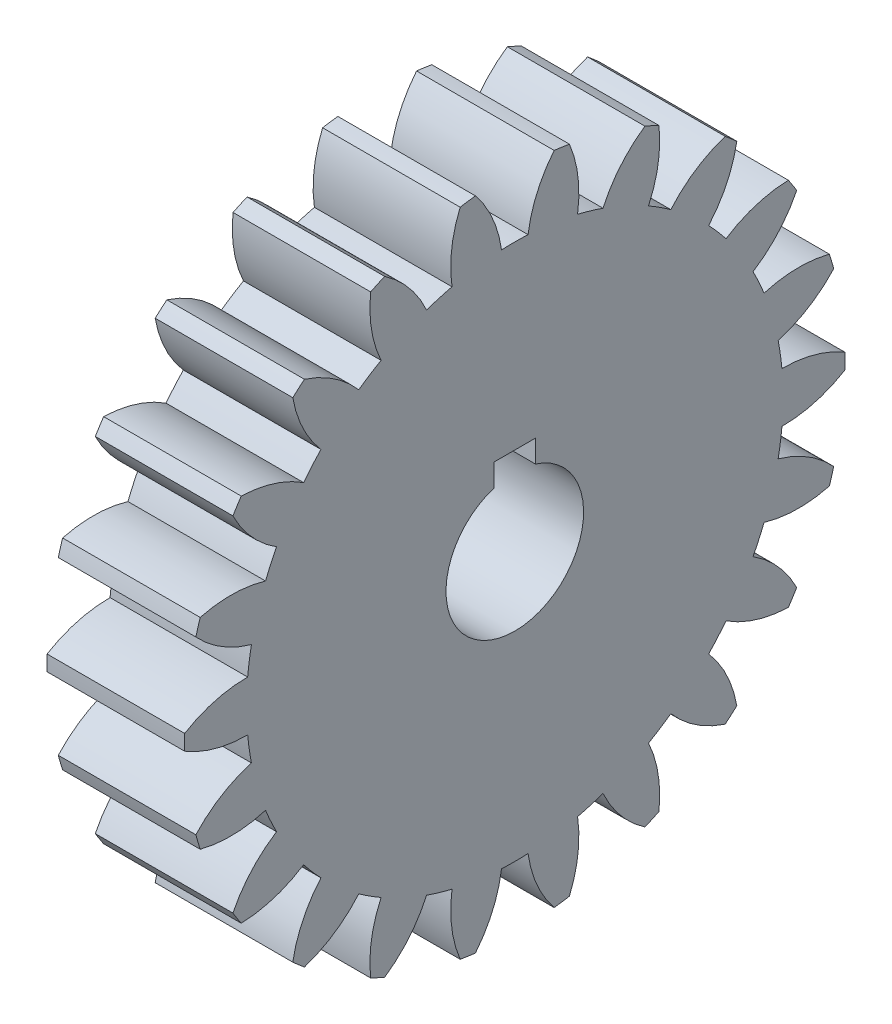
SolidWorks part; units mm, degrees
ref_plane "Plane1" through (0, 0, 0) normal (0, 0, 1) x (1, 0, 0)
ref_plane "Plane2" through (0, 0, 0) normal (0, 1, 0) x (1, 0, 0)
ref_plane "Plane3" through (0, 0, 0) normal (1, 0, 0) x (0, 0, -1)
sketch "HoldingSke" plane through (0, 0, 0) normal (0, 1, 0) x (1, 0, 0)
  line L0 (0, 0) -> (0.2318, -0.0937)
  line L1 (-15, 0) -> (100, 0) construction
  line L2 (0, 0) -> (-2.1039, 2.3779)
  line L3 (0, 0) -> (-11.863, 4.5341)
  line L4 (0, 0) -> (8.0072, 3.2351)
  line L5 (0, 0) -> (-46.8476, -17.4728)
  line L6 (0, 0) -> (-16.5793, -11.1861)
  line L7 (-2.1039, 2.3779) -> (8.6586, 51.2059)
  line L8 (-76.2, 54.61) -> (-73.4, 54.61)
  line L9 (-71.009, 38.7566) -> (-53.1078, 45.2721)
  line L10 (-76.2, 71.12) -> (104.1128, 71.12)
  line L11 (0, 0) -> (-20, 0)
  line L12 (-76.2, 101.6) -> (-76.073, 101.6)
  line L13 (24.9733, 27.94) -> (52.9518, 28.4284)
  line L14 (24.9733, 27.94) -> (24.9743, 27.94)
  line L15 (24.9733, 27.94) -> (100.4006, 29.5858)
  line L16 (-63.627, -4) -> (-12.827, -4)
  circle A0 centre (0, 0) radius 10
  circle A1 centre (0, 0) radius 37.5
  circle A2 centre (0, 0) radius 37.5
  circle A3 centre (0, 0) radius 10
  dimension "MHD" = 75
  dimension "Hub_dia" = 75
  dimension "Bore" = 20
  dimension "MBD" = 20
  dimension "Num_teeth" = 22
  dimension "Pitch" = 0.25
  dimension "Overall_len" = 50
  dimension "Show_teeth" = 22
  dimension "Thickness" = 20
  dimension "OAL" = 50.0001
  dimension "T_dim" = 2.8
  dimension "Ap" = 20
  dimension "H" = 19.05
  dimension "Pitch_radius" = 180.3128
  dimension "Width" = 20
  dimension "Backlash" = 0.127
  dimension "Addendum_fac" = 1
  dimension "Dedendum_fac" = 1.25
  dimension "Clearance_fac" = 0.25
  dimension "Dedendum_add" = 0.001
  dimension "Module" = 4
sketch "BasProSke" plane through (0, 0, 0) normal (0, 1, 0) x (1, 0, 0)
  line L0 (-10, 0) -> (60, 0) construction
  line L1 (0, 0) -> (0, 48)
  line L2 (0, 0) -> (20, 0)
  line L3 (20, 0) -> (20, 48)
  line L4 (20, 48) -> (0, 48)
  dimension "Thickness" = 20
  dimension "Diameter" = 96
revolve "Base-Revolve" add sketch "BasProSke" angle 360 about L0
sketch "TooCutSke" plane through (0, 0, 0) normal (1, 0, 0) x (0, 0, -1)
  line L1 (0, 0) -> (0, 107) construction
  line L2 (0, 0) -> (-3.3611, 43.8714) construction
  line L3 (0, 0) -> (-12.4962, 86.9127) construction
  line L4 (-3.3611, 43.8714) -> (-6.2481, 43.4564) construction
  arc A0 (1.9256, 38.9514) -> (-1.9256, 38.9514) centre (0, 0) ccw
  arc A1 (5.7387, 47.6813) -> (-5.7387, 47.6813) centre (0, 0) ccw
  circle A2 centre (0, 0) radius 44 construction
  circle A3 centre (0, 0) radius 41.3465 construction
  arc A4 (-1.9256, 38.9514) -> (-5.7387, 47.6813) centre (-19.3589, 36.5344) ccw
  arc A5 (5.7387, 47.6813) -> (1.9256, 38.9514) centre (19.3589, 36.5344) ccw
  dimension "Root_dia" = 77.998
  dimension "Overcut_dia" = 96.0508
  dimension "Pitch_dia" = 88
  dimension "Base_dia" = 82.693
  dimension "Flank_rad" = 17.6
  dimension "Half_ang" = 8.182
  dimension "Half_CT" = 2.9167
extrude "ToothCut" cut sketch "TooCutSke" along normal through all
fillet "Breaks" [suppressed] radius 0.08
fillet "RootFillets" [suppressed] radius 1.001
pattern_circular "TeethCuts" count 22 every 16.364 about axis through (-10, 0, 0) along (1, 0, 0) of "ToothCut", "RootFillets", "Breaks"
sketch "HubNeaOneSke" plane through (0, 0, 0) normal (-1, 0, 0) x (0, 0, 1)
  circle A0 centre (0, 0) radius 37.5
  dimension "Diameter" = 75
extrude "HubNearOne" [suppressed] add sketch "HubNeaOneSke" along normal blind 30.0001
sketch "HubNeaBotSke" plane through (0, 0, 0) normal (-1, 0, 0) x (0, 0, 1)
  circle A0 centre (0, 0) radius 37.5
  dimension "Diameter" = 75
extrude "HubNearBoth" [suppressed] add sketch "HubNeaBotSke" along normal blind 15
ref_plane "FarPln" through (20, 0, 0) normal (1, 0, 0) x (0, 0, -1)
sketch "HubFarSke" plane through (20, 0, 0) normal (1, 0, 0) x (0, 0, -1)
  circle A0 centre (0, 0) radius 37.5
  dimension "Diameter" = 75
extrude "HubFar" [suppressed] add sketch "HubFarSke" along normal blind 15
sketch "BorSke" plane through (0, 0, 0) normal (1, 0, 0) x (0, 0, -1)
  circle A0 centre (0, 0) radius 10
  dimension "Diameter" = 20
extrude "Bore" cut sketch "BorSke" along normal mid plane 100.0001
sketch "KeySke" plane through (0, 0, 0) normal (1, 0, 0) x (0, 0, -1)
  line L0 (-3, 0) -> (-3, 12.8)
  line L1 (-3, 12.8) -> (3, 12.8)
  line L2 (3, 12.8) -> (3, 0)
  line L3 (0, 0) -> (0, 34) construction
  line L4 (-3, 0) -> (3, 0)
  dimension "Offset" = 12.8
  dimension "Width" = 6
extrude "Keyway" cut sketch "KeySke" along normal mid plane 100.0001
pattern_circular "Keyway2" [suppressed] count 2 every 90 about axis through (-10, 0, 0) along (1, 0, 0)
sketch "Çizim1" plane through (20, 0, 0) normal (1, 0, 0) x (0, 0, -1)
  circle A0 centre (0, 0) radius 44 construction
  dimension "D1" = 88
equation "' \"Module@HoldingSke\" = 6.35"
equation "' \"Num_teeth@HoldingSke\" = 12"
equation "' \"Ap@HoldingSke\" =  20"
equation "' \"Ap@HoldingSke\" = 20"
equation "' \"Width@HoldingSke\" = 0.5 * 25.4"
equation "' \"Hub_dia@HoldingSke\"= 1 * 25.4"
equation "' \"Hub_dia@HoldingSke\" = 1 * 25.4"
equation "' \"Overall_len@HoldingSke\" = 1.0 * 25.4"
equation "' \"Bore@HoldingSke\" = 0.75 * 25.4"
equation "' \"T_dim@HoldingSke\" = 0.1 * 25.4"
equation "' \"Width@KeySke\" = 0.25 * 25.4"
equation "' \"Show_teeth@HoldingSke\" = 13"
equation "' \"Backlash@HoldingSke\" = 0.009 * 25.4"
equation "' \"Addendum_fac@HoldingSke\" = 1.0"
equation "' \"Dedendum_fac@HoldingSke\" = 1.25"
equation "' \"Dedendum_add@HoldingSke\" = 0.00005 * 25.4"
equation "' \"Clearance_fac@HoldingSke\" = 0.25"
equation "\"Pitch@HoldingSke\" = 1 / \"Module@HoldingSke\""
equation "\"Overcut_dia@TooCutSke\" = (\"Num_teeth@HoldingSke\" + 2 * \"Addendum_fac@HoldingSke\") / \"Pitch@HoldingSke\" + 0.002 * 25.4"
equation "\"Pitch_dia@TooCutSke\" = \"Num_teeth@HoldingSke\" / \"Pitch@HoldingSke\""
equation "\"Base_dia@TooCutSke\" = \"Num_teeth@HoldingSke\" / \"Pitch@HoldingSke\" * cos((\"Ap@HoldingSke\"  * 3.14159265 / 180))"
equation "\"Root_dia@TooCutSke\" = (\"Num_teeth@HoldingSke\" + 2) / \"Pitch@HoldingSke\" - 2 * (\"Addendum_fac@HoldingSke\" + \"Dedendum_fac@HoldingSke\") / \"Pitch@HoldingSke\" - \"Dedendum_add@HoldingSke\" * 2"
equation "\"Half_ang@TooCutSke\" = 180 / \"Num_teeth@HoldingSke\""
equation "\"Half_CT@TooCutSke\" = \"Num_teeth@HoldingSke\" / \"Pitch@HoldingSke\" * sin((3.14159265 / 2 / \"Num_teeth@HoldingSke\")) / 2 - 7 * \"Backlash@HoldingSke\" / 4"
equation "\"Flank_rad@TooCutSke\" = \"Num_teeth@HoldingSke\" / \"Pitch@HoldingSke\" / 5"
equation "\"Radius@RootFillets\" = \"Clearance_fac@HoldingSke\" / \"Pitch@HoldingSke\" + \"Dedendum_add@HoldingSke\""
equation "\"Break_rad@Breaks\" = 0.02 / \"Pitch@HoldingSke\""
equation "\"Thickness@HoldingSke\" = \"Width@HoldingSke\""
equation "\"OAL@HoldingSke\" = \"Thickness@HoldingSke\""
equation "\"MHD@HoldingSke\" = (\"Num_teeth@HoldingSke\" + 2) / \"Pitch@HoldingSke\" - 2 * (\"Addendum_fac@HoldingSke\" + \"Dedendum_fac@HoldingSke\")  / \"Pitch@HoldingSke\" - \"Dedendum_add@HoldingSke\" * 2"
equation "\"MBD@HoldingSke\" = (\"Num_teeth@HoldingSke\" + 2) / \"Pitch@HoldingSke\" - 2 * (\"Addendum_fac@HoldingSke\" + \"Dedendum_fac@HoldingSke\")  / \"Pitch@HoldingSke\" - \"Dedendum_add@HoldingSke\" * 2 - 0.002 * 25.4"
equation "\"MHD@HoldingSke\" = ((sgn( \"MHD@HoldingSke\" - \"Hub_dia@HoldingSke\" )-1)*( \"MHD@HoldingSke\" - \"Hub_dia@HoldingSke\" ))/-2+ \"Hub_dia@HoldingSke\""
equation "\"MBD@HoldingSke\" = ((sgn( \"MBD@HoldingSke\" - \"Bore@HoldingSke\" )-1)*( \"MBD@HoldingSke\" - \"Bore@HoldingSke\" ))/-2+ \"Bore@HoldingSke\""
equation "\"OAL@HoldingSke\" = ((sgn( \"OAL@HoldingSke\" - \"Overall_len@HoldingSke\" )+1)*( \"OAL@HoldingSke\" - \"Overall_len@HoldingSke\" ))/2 + \"Overall_len@HoldingSke\" + 0.000002 * 25.4"
equation "\"Num_teeth@TeethCuts\" = int( \"Show_teeth@HoldingSke\" ) + 1"
equation "\"Num_teeth@TeethCuts\" = ((sgn( \"Num_teeth@TeethCuts\" - \"Num_teeth@HoldingSke\" )-1)*( \"Num_teeth@TeethCuts\" - \"Num_teeth@HoldingSke\" ))/-2+ \"Num_teeth@HoldingSke\""
equation "\"Num_teeth@TeethCuts\" = ((sgn( \"Num_teeth@TeethCuts\" - 2.0)+1)*( \"Num_teeth@TeethCuts\" - 2.0))/2 +2.0"
equation "\"Angle@TeethCuts\" = 360.0 / \"Num_teeth@HoldingSke\""
equation "\"Diameter@BasProSke\" = (\"Num_teeth@HoldingSke\" + 2 * \"Addendum_fac@HoldingSke\") / \"Pitch@HoldingSke\""
equation "\"Thickness@BasProSke\"  = \"Thickness@HoldingSke\""
equation "' \"Fillet_rad@BasProSke\" =  \"Thickness@HoldingSke\" * 0.05"
equation "' \"Fillet_rad@BasProSke\" = \"Thickness@HoldingSke\" * 0.05"
equation "\"MHD@HoldingSke\" = ((sgn( \"MHD@HoldingSke\" - \"Root_dia@TooCutSke\" )-1)*( \"MHD@HoldingSke\" - \"Root_dia@TooCutSke\" ))/-2+ \"Root_dia@TooCutSke\""
equation "\"Diameter@HubNeaOneSke\" = \"MHD@HoldingSke\""
equation "\"Length@HubNearOne\" = \"OAL@HoldingSke\" - \"Thickness@BasProSke\""
equation "\"Diameter@HubNeaBotSke\" = \"MHD@HoldingSke\""
equation "\"Length@HubNearBoth\" = ( \"OAL@HoldingSke\" - \"Thickness@BasProSke\" ) / 2.0"
equation "\"Thickness@FarPln\" = \"Thickness@BasProSke\""
equation "\"Diameter@HubFarSke\" = \"MHD@HoldingSke\""
equation "\"Length@HubFar\" = ( \"OAL@HoldingSke\" - \"Thickness@BasProSke\" ) / 2.0"
equation "\"Diameter@BorSke\" = \"MBD@HoldingSke\""
equation "\"D1@Bore\" = \"OAL@HoldingSke\" * 2.0"
equation "\"D1@Keyway\" = \"OAL@HoldingSke\" * 2.0"
equation "\"Offset@KeySke\" = \"T_dim@HoldingSke\" + \"MBD@HoldingSke\" / 2.0"
